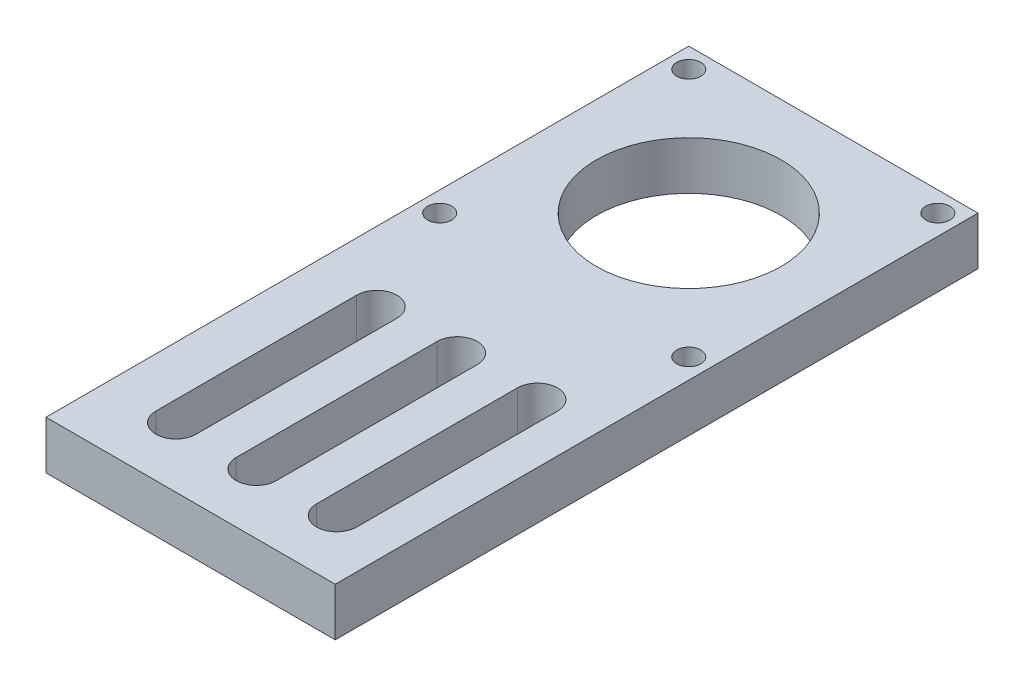
SolidWorks part; units mm, degrees
ref_plane "Front Plane" through (0, 0, 0) normal (0, 0, 1) x (1, 0, 0)
ref_plane "Top Plane" through (0, 0, 0) normal (0, 1, 0) x (1, 0, 0)
ref_plane "Right Plane" through (0, 0, 0) normal (1, 0, 0) x (0, 0, -1)
sketch "Sketch1" plane through (0, 0, 0) normal (0, 1, 0) x (1, 0, 0)
  line L1 (-18, -40) -> (18, -40)
  line L2 (-18, -40) -> (-18, 40)
  line L3 (-18, 40) -> (18, 40)
  line L4 (18, -40) -> (18, 40)
  line L5 (-18, -40) -> (18, 40) construction
  line L6 (-18, 40) -> (18, -40) construction
  line L7 (15.5, 6.5) -> (-15.5, 6.5) construction
  line L8 (15.5, 6.5) -> (15.5, 37.5) construction
  line L9 (15.5, 37.5) -> (-15.5, 37.5) construction
  line L10 (-15.5, 6.5) -> (-15.5, 37.5) construction
  line L11 (15.5, 6.5) -> (-15.5, 37.5) construction
  line L12 (15.5, 37.5) -> (-15.5, 6.5) construction
  line L14 (-1.8272, -32.5) -> (-1.8272, -7.5)
  line L16 (3.1728, -32.5) -> (3.1728, -7.5)
  line L17 (-1.8272, -32.5) -> (3.1728, -7.5) construction
  line L18 (-1.8272, -7.5) -> (3.1728, -32.5) construction
  line L20 (8.1728, -32.5) -> (8.1728, -7.5)
  line L22 (13.1728, -32.5) -> (13.1728, -7.5)
  line L23 (8.1728, -32.5) -> (13.1728, -7.5) construction
  line L24 (8.1728, -7.5) -> (13.1728, -32.5) construction
  line L26 (-6.8272, -32.5) -> (-6.8272, -7.5)
  line L28 (-11.8272, -32.5) -> (-11.8272, -7.5)
  line L29 (-6.8272, -32.5) -> (-11.8272, -7.5) construction
  line L30 (-6.8272, -7.5) -> (-11.8272, -32.5) construction
  circle A0 centre (0, 22) radius 11.5
  circle A1 centre (-15.5, 37.5) radius 1.5
  circle A2 centre (15.5, 37.5) radius 1.5
  circle A3 centre (15.5, 6.5) radius 1.5
  circle A4 centre (-15.5, 6.5) radius 1.5
  arc A5 (-11.8272, -7.5) -> (-6.8272, -7.5) centre (-9.3272, -7.5) cw
  arc A6 (-6.8272, -32.5) -> (-11.8272, -32.5) centre (-9.3272, -32.5) cw
  arc A7 (-1.8272, -32.5) -> (3.1728, -32.5) centre (0.6728, -32.5) ccw
  arc A8 (-1.8272, -7.5) -> (3.1728, -7.5) centre (0.6728, -7.5) cw
  arc A9 (8.1728, -7.5) -> (13.1728, -7.5) centre (10.6728, -7.5) cw
  arc A10 (8.1728, -32.5) -> (13.1728, -32.5) centre (10.6728, -32.5) ccw
  point P0 (0, 0)
  point P16 (0.6728, -20)
  point P21 (10.6728, -20)
  point P26 (-9.3272, -20)
  dimension "D1" = 23
  dimension "D5" = 31
  dimension "D6" = 3
  dimension "D2" = 22
  dimension "D3" = 80
  dimension "D4" = 36
  dimension "D7" = 2.5
  dimension "D8" = 2.5
  dimension "D9" = 2.5
  dimension "D10" = 10
  dimension "D11" = 10
  dimension "D12" = 20
  dimension "D13" = 25
extrude "Boss-Extrude1" add sketch "Sketch1" along normal blind 6
